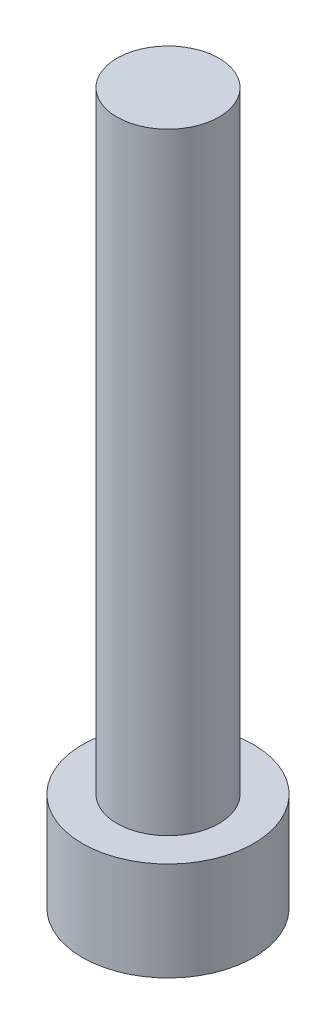
SolidWorks part; units mm, degrees
ref_plane "前视基准面" through (0, 0, 0) normal (0, 0, 1) x (1, 0, 0)
ref_plane "上视基准面" through (0, 0, 0) normal (0, 1, 0) x (1, 0, 0)
ref_plane "右视基准面" through (0, 0, 0) normal (1, 0, 0) x (0, 0, -1)
sketch "草图1" plane through (0, 0, 0) normal (0, 1, 0) x (1, 0, 0)
  circle A0 centre (0, 0) radius 4.2
extrude "凸台-拉伸1" add sketch "草图1" along normal blind 4.84
sketch "草图2" plane through (0, 4.84, 0) normal (0, 1, 0) x (1, 0, 0)
  circle A0 centre (0, 0) radius 2.5
extrude "凸台-拉伸2" add sketch "草图2" along normal blind 30
sketch "草图3" plane through (0, 0, 0) normal (0, -1, 0) x (1, 0, 0)
  line L1 (2.3, 0) -> (1.15, 1.9919)
  line L2 (1.15, 1.9919) -> (-1.15, 1.9919)
  line L3 (-1.15, 1.9919) -> (-2.3, 0)
  line L4 (-2.3, 0) -> (-1.15, -1.9919)
  line L5 (-1.15, -1.9919) -> (1.15, -1.9919)
  line L6 (1.15, -1.9919) -> (2.3, 0)
  circle A0 centre (0, 0) radius 1.9919 construction
extrude "切除-拉伸1" cut sketch "草图3" against normal blind 3.4
